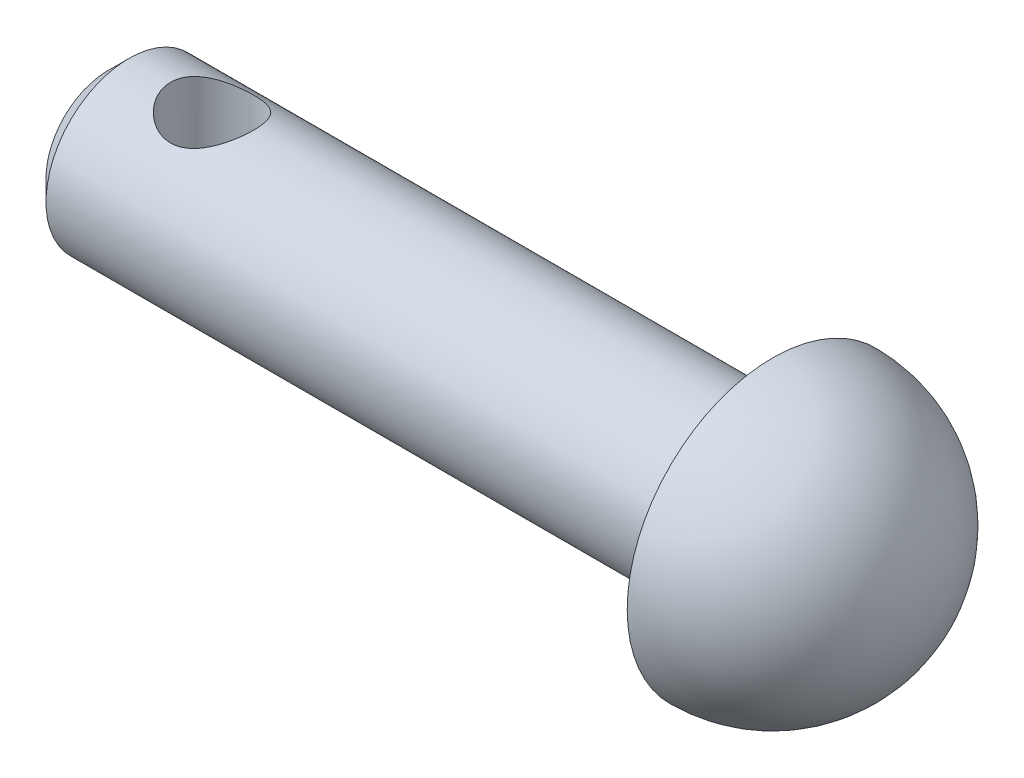
SolidWorks part; units mm, degrees
ref_plane "Front Plane" through (0, 0, 0) normal (0, 0, 1) x (1, 0, 0)
ref_plane "Top Plane" through (0, 0, 0) normal (0, 1, 0) x (1, 0, 0)
ref_plane "Right Plane" through (0, 0, 0) normal (1, 0, 0) x (0, 0, -1)
sketch "Sketch3" plane through (0, 0, 0) normal (1, 0, 0) x (0, 0, -1)
  circle A0 centre (0, 0) radius 2
extrude "Boss-Extrude1" add sketch "Sketch3" along normal blind 16
chamfer "Chamfer1" distance 0.5 angle 45 1 edges at (0, 0, -2)
sketch "Sketch4" plane through (0, 0, 0) normal (0, 1, 0) x (1, 0, 0)
  line L0 (16, -2) -> (16, 2) construction
  circle A0 centre (2.5, 0) radius 1
  dimension "D1" = 13.5
extrude "Cut-Extrude1" cut sketch "Sketch4" against normal through all both and the other way through all
sketch "Sketch5" plane through (0, 0, 0) normal (0, 1, 0) x (1, 0, 0)
  line L0 (16, 0) -> (16, 3.5)
  line L1 (16, -2) -> (16, 2) construction
  line L2 (16, 0) -> (19.5, 0)
  arc A0 (16, 3.5) -> (19.5, 0) centre (16, 0) cw
revolve "Revolve1" add sketch "Sketch5" angle 360 about L2
